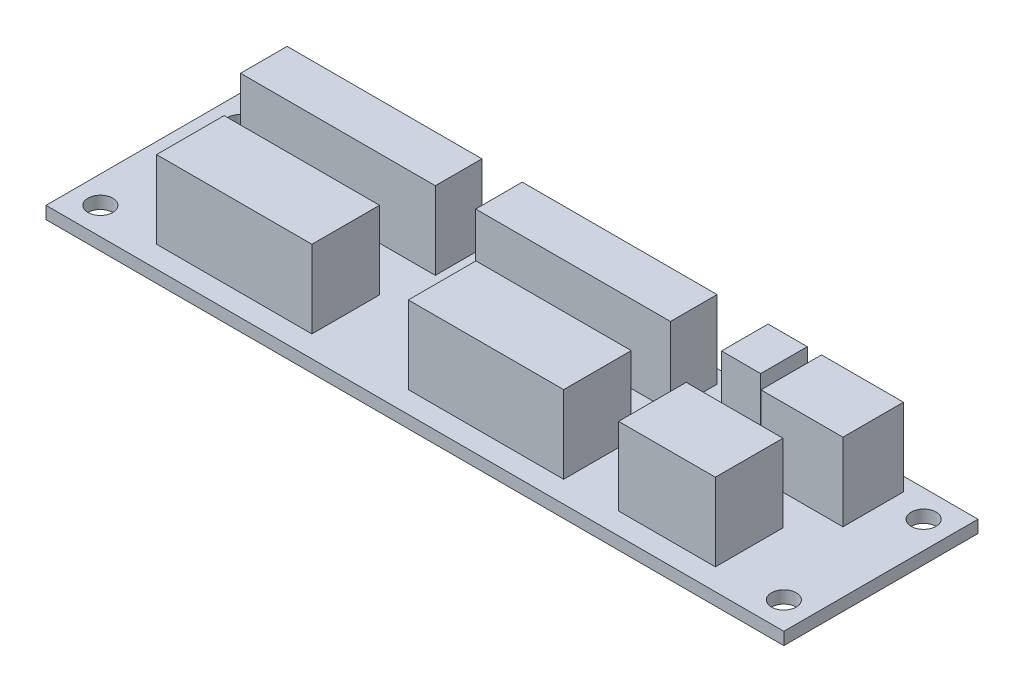
SolidWorks part; units mm, degrees
ref_plane "Front Plane" through (0, 0, 0) normal (0, 0, 1) x (1, 0, 0)
ref_plane "Top Plane" through (0, 0, 0) normal (0, 1, 0) x (1, 0, 0)
ref_plane "Right Plane" through (0, 0, 0) normal (1, 0, 0) x (0, 0, -1)
sketch "Sketch1" plane through (0, 0, 0) normal (0, 1, 0) x (1, 0, 0)
  line L0 (18, 9.5) -> (18, -15.5) construction
  line L1 (-29.5, 9.5) -> (65.5, 9.5)
  line L2 (-29.5, 9.5) -> (-29.5, -15.5)
  line L3 (-29.5, -15.5) -> (65.5, -15.5)
  line L4 (65.5, 9.5) -> (65.5, -15.5)
  line L5 (-29.5, -3) -> (65.5, -3) construction
  circle A0 centre (-26, 6) radius 1.6
  circle A1 centre (62, 6) radius 1.6
  circle A2 centre (62, -12) radius 1.6
  circle A3 centre (-26, -12) radius 1.6
  point P0 (0, 0)
  dimension "D3" = 3.2
  dimension "D1" = 25
  dimension "D2" = 95
  dimension "D4" = 88
  dimension "D5" = 18
extrude "Boss-Extrude1" add sketch "Sketch1" along normal blind 1.6
sketch "Sketch2" plane through (0, 1.6, 0) normal (0, 1, 0) x (1, 0, 0)
  line L0 (41.4535, -8.3746) -> (53.9112, -8.3746) construction
  line L1 (-21.7018, 7.7492) -> (3.3767, 7.7492)
  line L2 (-21.7018, 7.7492) -> (-21.7018, 1.7492)
  line L3 (-21.7018, 1.7492) -> (3.3767, 1.7492)
  line L4 (3.3767, 7.7492) -> (3.3767, 1.7492)
  line L5 (-21.7018, 4.7492) -> (3.3767, 4.7492) construction
  line L6 (8.5734, 4.7492) -> (33.6519, 4.7492) construction
  line L7 (8.5734, 7.7492) -> (33.6519, 7.7492)
  line L8 (8.5734, 7.7492) -> (8.5734, 1.7492)
  line L9 (8.5734, 1.7492) -> (33.6519, 1.7492)
  line L10 (33.6519, 7.7492) -> (33.6519, 1.7492)
  line L11 (40.2248, 4.7492) -> (45.2706, 4.7492) construction
  line L12 (14.3771, -8.3746) -> (34.3771, -8.3746) construction
  line L13 (40.2248, 7.7492) -> (45.2706, 7.7492)
  line L14 (40.2248, 7.7492) -> (40.2248, 1.7492)
  line L15 (40.2248, 1.7492) -> (45.2706, 1.7492)
  line L16 (45.2706, 7.7492) -> (45.2706, 1.7492)
  line L17 (-18.0383, -4.0246) -> (1.9617, -4.0246)
  line L18 (-18.0383, -4.0246) -> (-18.0383, -12.7246)
  line L19 (47.1055, 7.7492) -> (57.656, 7.7492)
  line L20 (47.1055, 7.7492) -> (47.1055, -0.049)
  line L21 (47.1055, -0.049) -> (57.656, -0.049)
  line L22 (57.656, 7.7492) -> (57.656, -0.049)
  line L23 (-29.5, 9.5) -> (-29.5, -15.5) construction
  line L26 (-18.0383, -12.7246) -> (1.9617, -12.7246)
  line L27 (1.9617, -4.0246) -> (1.9617, -12.7246)
  line L28 (-18.0383, -8.3746) -> (1.9617, -8.3746) construction
  line L29 (41.4535, -4.0246) -> (53.9112, -4.0246)
  line L30 (14.3771, -4.0246) -> (34.3771, -4.0246)
  line L31 (14.3771, -4.0246) -> (14.3771, -12.7246)
  line L32 (14.3771, -12.7246) -> (34.3771, -12.7246)
  line L33 (34.3771, -4.0246) -> (34.3771, -12.7246)
  line L34 (41.4535, -4.0246) -> (41.4535, -12.7246)
  line L35 (41.4535, -12.7246) -> (53.9112, -12.7246)
  line L36 (53.9112, -4.0246) -> (53.9112, -12.7246)
  dimension "D1" = 6
  dimension "D2" = 7.7982
  dimension "D3" = 32.8767
  dimension "D4" = 38.0734
  dimension "D5" = 69.7248
  dimension "D6" = 7.7982
  dimension "D7" = 74.7706
  dimension "D8" = 76.6055
  dimension "D9" = 8.7
  dimension "D10" = 87.156
extrude "Boss-Extrude2" add sketch "Sketch2" along normal blind 10
